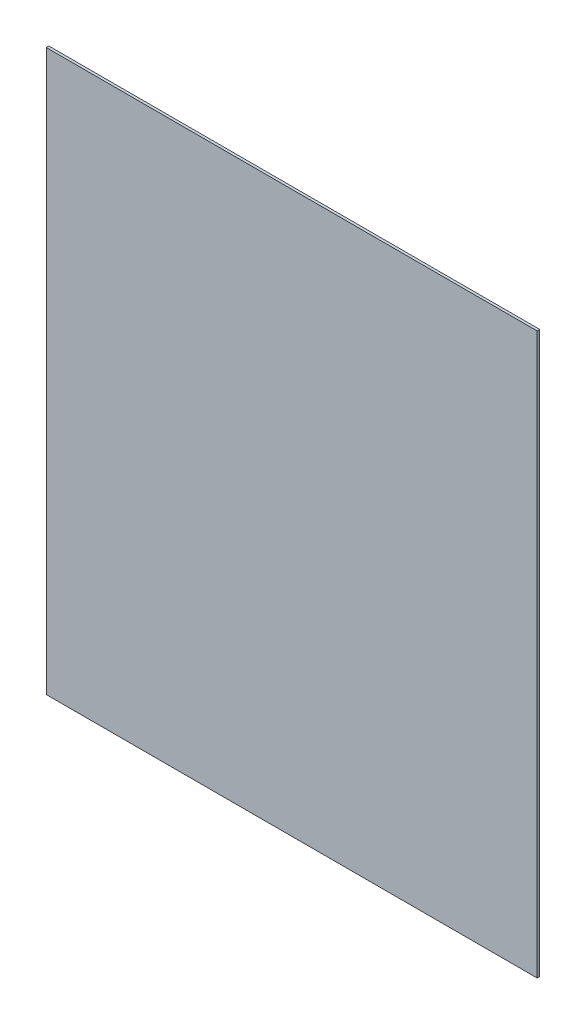
SolidWorks part; units mm, degrees
ref_plane "Přední rovina" through (0, 0, 0) normal (0, 0, 1) x (1, 0, 0)
ref_plane "Horní rovina" through (0, 0, 0) normal (0, 1, 0) x (1, 0, 0)
ref_plane "Pravá rovina" through (0, 0, 0) normal (1, 0, 0) x (0, 0, -1)
sketch "Skica1" plane through (0, 0, 0) normal (0, 0, 1) x (1, 0, 0)
  line L1 (-282.5, 322.5) -> (282.5, 322.5)
  line L2 (-282.5, 322.5) -> (-282.5, -322.5)
  line L3 (-282.5, -322.5) -> (282.5, -322.5)
  line L4 (282.5, 322.5) -> (282.5, -322.5)
  line L5 (-282.5, 322.5) -> (282.5, -322.5) construction
  line L6 (-282.5, -322.5) -> (282.5, 322.5) construction
  point P0 (0, 0)
  dimension "D1" = 565
  dimension "D2" = 645
extrude "Přidat vysunutím1" add sketch "Skica1" along normal blind 3
